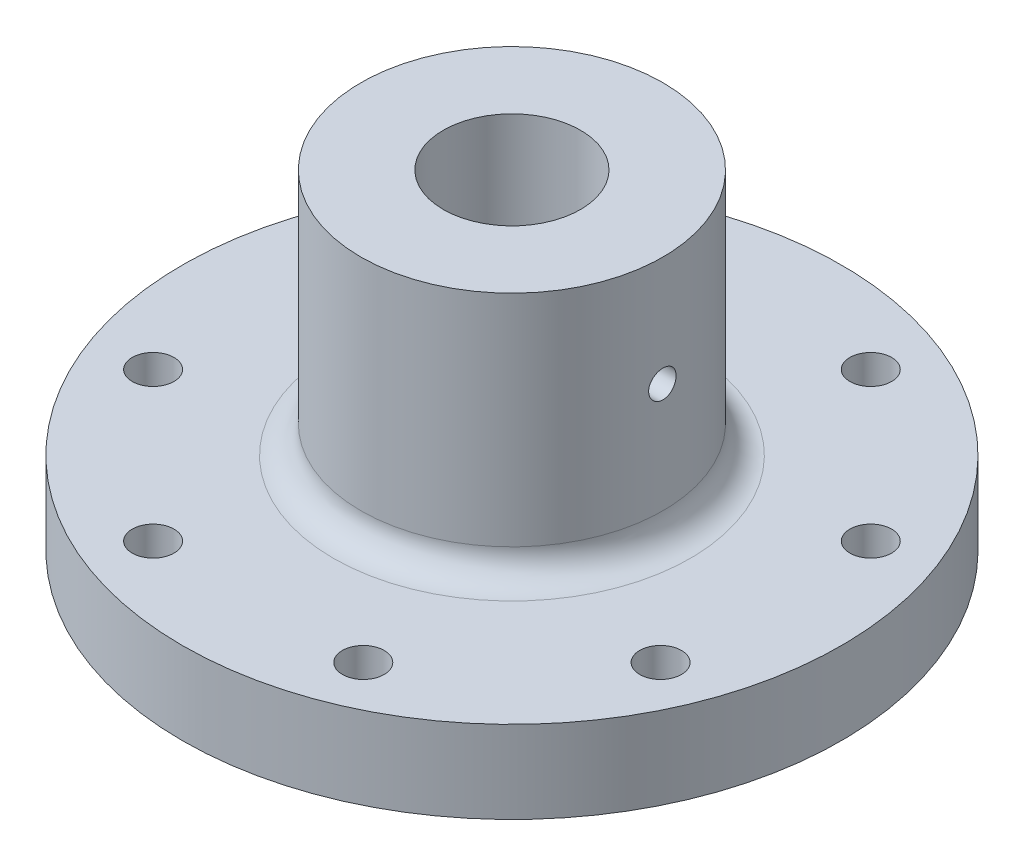
SolidWorks part; units mm, degrees
material "6061-T6 (SS)"
ref_plane "Front Plane" through (0, 0, 0) normal (0, 0, 1) x (1, 0, 0)
ref_plane "Top Plane" through (0, 0, 0) normal (0, 1, 0) x (1, 0, 0)
ref_plane "Right Plane" through (0, 0, 0) normal (1, 0, 0) x (0, 0, -1)
sketch "Sketch1" plane through (0, 0, 0) normal (0, 1, 0) x (1, 0, 0)
  circle A0 centre (0, 0) radius 38.1
  circle A1 centre (0, 0) radius 7.9375
  dimension "D1" = 76.2
  dimension "D2" = 15.875
extrude "Boss-Extrude1" add sketch "Sketch1" along normal blind 38.1
hole_wizard "#10-32 Tapped Hole1" positions "Sketch3" profile "Sketch2" tap size "#10-32" standard "Ansi Inch" end condition through all
sketch "Sketch3" plane through (0, 38.1, 0) normal (0, 1, 0) x (-1, 0, 0)
  line L0 (38.1, 0) -> (0, 0) construction
  line L1 (0, 0) -> (29.3332, -12.1502) construction
  circle A0 centre (0, 0) radius 38.1 construction
  point P0 (29.3332, -12.1502)
  dimension "D1" = 31.75
  dimension "D2" = 22.5
sketch "Sketch2" plane through (-29.3332, 38.1, -12.1502) normal (1, 0, 0) x (0, 0, 1)
  line L0 (0, 0) -> (0, 38.1)
  line L1 (0, 38.1) -> (2.413, 38.1)
  line L2 (2.413, 38.1) -> (2.413, 0)
  line L5 (2.413, 0) -> (0, 0)
  line L11 (0, -6.35) -> (0, 107.95) construction
  dimension "Thread Major Dia." = 4.826
  dimension "Thru Tap Drill Depth" = 38.1
pattern_circular "CirPattern1" count 8 over 360 about axis through (0, 0, 0) along (0, 1, 0) of "#10-32 Tapped Hole1"
sketch "Sketch7" plane through (0, 38.1, 0) normal (0, 1, 0) x (1, 0, 0)
  circle A0 centre (0, 0) radius 17.4625
  circle A1 centre (0, 0) radius 7.9375 construction
  dimension "D1" = 9.525
extrude "Cut-Extrude2" cut sketch "Sketch7" against normal offset from surface (28.575 mm away) 9.525 flip side to cut up to face at (-29.3332, 0, 14.5632)
fillet "Fillet1" radius 3.175 1 edges at (0, 9.525, 17.4625)
sketch "Sketch8" plane through (0, 0, 0) normal (1, 0, 0) x (0, 0, -1)
  line L0 (17.4625, 38.1) -> (-17.4625, 38.1) construction
  circle A0 centre (0, 25.4) radius 1.5875
  dimension "D1" = 3.175
  dimension "D2" = 12.7
extrude "Cut-Extrude3" cut sketch "Sketch8" against normal through all both and the other way through all contours A0
